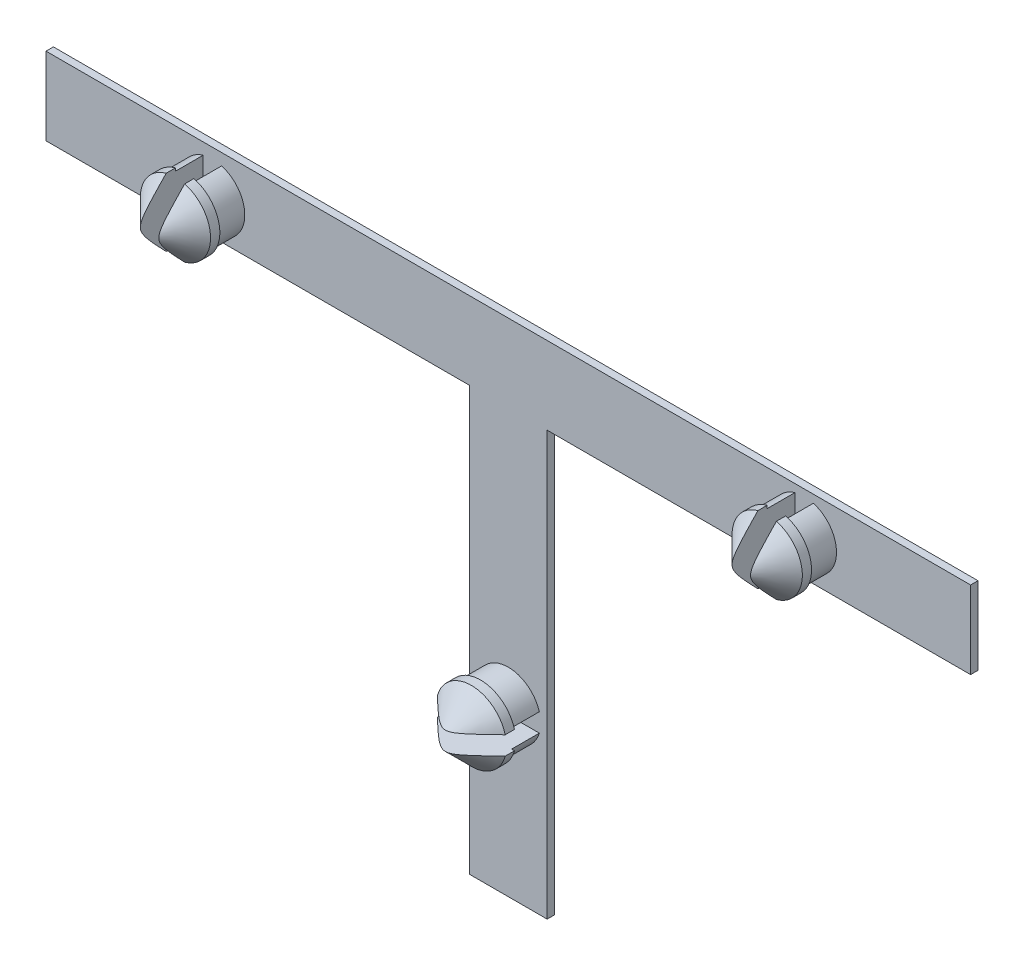
SolidWorks part; units mm, degrees
ref_plane "Přední rovina" through (0, 0, 0) normal (0, 0, 1) x (1, 0, 0)
ref_plane "Horní rovina" through (0, 0, 0) normal (0, 1, 0) x (1, 0, 0)
ref_plane "Pravá rovina" through (0, 0, 0) normal (1, 0, 0) x (0, 0, -1)
sketch "Skica2" plane through (0, 0, 0) normal (0, 0, 1) x (1, 0, 0)
  line L1 (-25, 2.1) -> (25, 2.1)
  line L2 (-25, 2.1) -> (-25, -2.1)
  line L3 (-25, -2.1) -> (25, -2.1)
  line L4 (25, 2.1) -> (25, -2.1)
  line L5 (-25, 2.1) -> (25, -2.1) construction
  line L6 (-25, -2.1) -> (25, 2.1) construction
  point P0 (0, 0)
  point P5 (-1, -0.2)
  dimension "D1" = 4.2
  dimension "D2" = 50
extrude "Přidat vysunutím2" add sketch "Skica2" along normal blind 0.4
sketch "Skica3" plane through (0, 0, 0.4) normal (0, 0, 1) x (1, 0, 0)
  line L0 (-25, 2.1) -> (-25, -2.1) construction
  line L1 (25, -2.1) -> (25, 2.1) construction
  line L2 (25, 2.1) -> (-25, 2.1) construction
  line L3 (-25, -2.1) -> (25, -2.1) construction
  circle A0 centre (-16, -0.2) radius 1.75
  circle A1 centre (16, 0) radius 1.75
  dimension "D1" = 3.5
  dimension "D3" = 3.5
  dimension "D2" = 9
  dimension "D4" = 9
  dimension "D5" = 2.3
  dimension "D6" = 1.9
extrude "Přidat vysunutím3" add sketch "Skica3" along normal blind 1.5
sketch "Skica5" plane through (0, 0, 1.9) normal (0, 0, 1) x (1, 0, 0)
  circle A0 centre (-16, -0.2) radius 1.9
  circle A1 centre (16, 0) radius 1.9
  dimension "D1" = 3.8
  dimension "D2" = 3.8
extrude "Přidat vysunutím5" add sketch "Skica5" along normal blind 2
chamfer "Zkosení2" distance 1.5 angle 45 2 edges at (17.9, 0, 3.9) (-14.1, -0.2, 3.9)
sketch "Skica7" plane through (0, 0, 3.9) normal (0, 0, 1) x (1, 0, 0)
  line L1 (-15.5, 2.3) -> (-16.5, 2.3)
  line L2 (-15.5, 2.3) -> (-15.5, -2.7)
  line L3 (-15.5, -2.7) -> (-16.5, -2.7)
  line L4 (-16.5, 2.3) -> (-16.5, -2.7)
  line L5 (-15.5, 2.3) -> (-16.5, -2.7) construction
  line L6 (-15.5, -2.7) -> (-16.5, 2.3) construction
  line L7 (15.5, 2.5) -> (16.5, 2.5)
  line L8 (15.5, 2.5) -> (15.5, -2.5)
  line L9 (15.5, -2.5) -> (16.5, -2.5)
  line L10 (16.5, 2.5) -> (16.5, -2.5)
  line L11 (15.5, 2.5) -> (16.5, -2.5) construction
  line L12 (15.5, -2.5) -> (16.5, 2.5) construction
  point P0 (-16, -0.2)
  point P5 (16, 0)
  dimension "D1" = 5
  dimension "D2" = 1
  dimension "D3" = 5
  dimension "D4" = 1
extrude "Odebrat vysunutím1" cut sketch "Skica7" against normal blind 3.5
sketch "Skica8" plane through (0, 0, 0) normal (0, 0, -1) x (-1, 0, 0)
  line L0 (25, -2.1) -> (-25, -2.1) construction
  line L1 (-2.1, -2.1) -> (2.1, -2.1)
  line L2 (-2.1, -2.1) -> (-2.1, -25)
  line L3 (-2.1, -25) -> (2.1, -25)
  line L4 (2.1, -2.1) -> (2.1, -25)
  line L5 (-25, -2.1) -> (-25, 2.1) construction
  line L6 (25, 2.1) -> (25, -2.1) construction
  dimension "D1" = 22.9
  dimension "D2" = 4.2
  dimension "D3" = 22.9
  dimension "D4" = 22.9
extrude "Přidat vysunutím6" add sketch "Skica8" against normal blind 0.4
sketch "Skica9" plane through (0, 0, 0.4) normal (0, 0, 1) x (1, 0, 0)
  line L0 (2.1, -25) -> (-2.1, -25) construction
  circle A0 centre (0, -16) radius 1.75
  dimension "D1" = 3.5
  dimension "D2" = 9
extrude "Přidat vysunutím7" add sketch "Skica9" along normal blind 1.5
sketch "Skica10" plane through (0, 0, 1.9) normal (0, 0, 1) x (1, 0, 0)
  line L0 (2.1, -25) -> (-2.1, -25) construction
  circle A0 centre (0, -16) radius 1.9
  dimension "D1" = 3.8
  dimension "D2" = 9
extrude "Přidat vysunutím8" add sketch "Skica10" along normal blind 2
chamfer "Zkosení3" distance 1.5 angle 45 1 edges at (1.9, -16, 3.9)
sketch "Skica12" plane through (0, 0, 3.9) normal (0, 0, 1) x (1, 0, 0)
  line L1 (-2.5, -15.5) -> (2.5, -15.5)
  line L2 (-2.5, -15.5) -> (-2.5, -16.5)
  line L3 (-2.5, -16.5) -> (2.5, -16.5)
  line L4 (2.5, -15.5) -> (2.5, -16.5)
  line L5 (-2.5, -15.5) -> (2.5, -16.5) construction
  line L6 (-2.5, -16.5) -> (2.5, -15.5) construction
  point P0 (0, -16)
  dimension "D1" = 1
  dimension "D2" = 5
extrude "Odebrat vysunutím2" cut sketch "Skica12" against normal blind 3.5
equation "\"1.5.000mm\"=10"
